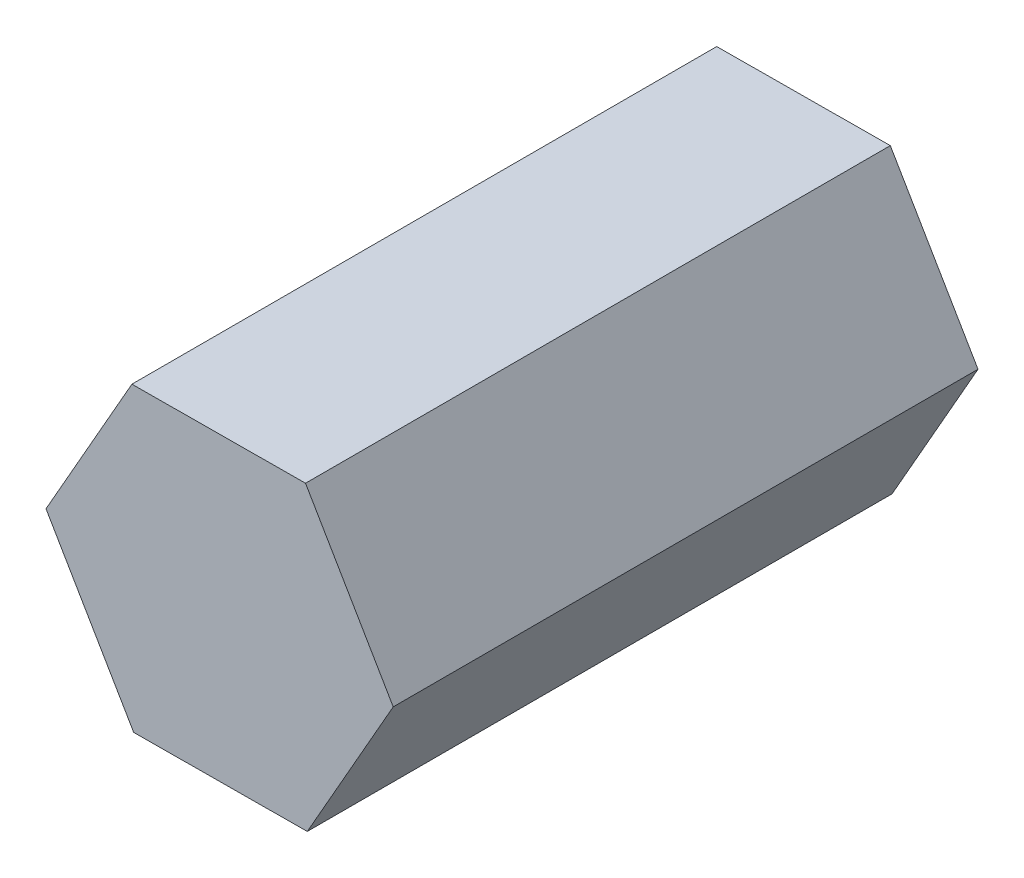
SolidWorks part; units mm, degrees
ref_plane "Piano frontale" through (0, 0, 0) normal (0, 0, 1) x (1, 0, 0)
ref_plane "Piano superiore" through (0, 0, 0) normal (0, 1, 0) x (1, 0, 0)
ref_plane "Piano destro" through (0, 0, 0) normal (1, 0, 0) x (0, 0, -1)
sketch "Schizzo1" plane through (0, 0, 0) normal (0, 0, 1) x (1, 0, 0)
  line L1 (-23.9905, 40.9964) -> (-47.4992, -0.2782)
  line L2 (-47.4992, -0.2782) -> (-23.5087, -41.2746)
  line L3 (-23.5087, -41.2746) -> (23.9905, -40.9964)
  line L4 (23.9905, -40.9964) -> (47.4992, 0.2782)
  line L5 (47.4992, 0.2782) -> (23.5087, 41.2746)
  line L6 (23.5087, 41.2746) -> (-23.9905, 40.9964)
  circle A0 centre (0, 0) radius 41.1362 construction
  dimension "D1" = 47.5
extrude "Estrusione-Estrusione1" add sketch "Schizzo1" along normal blind 160 contours L1 L2 L3 L4 L5 L6
